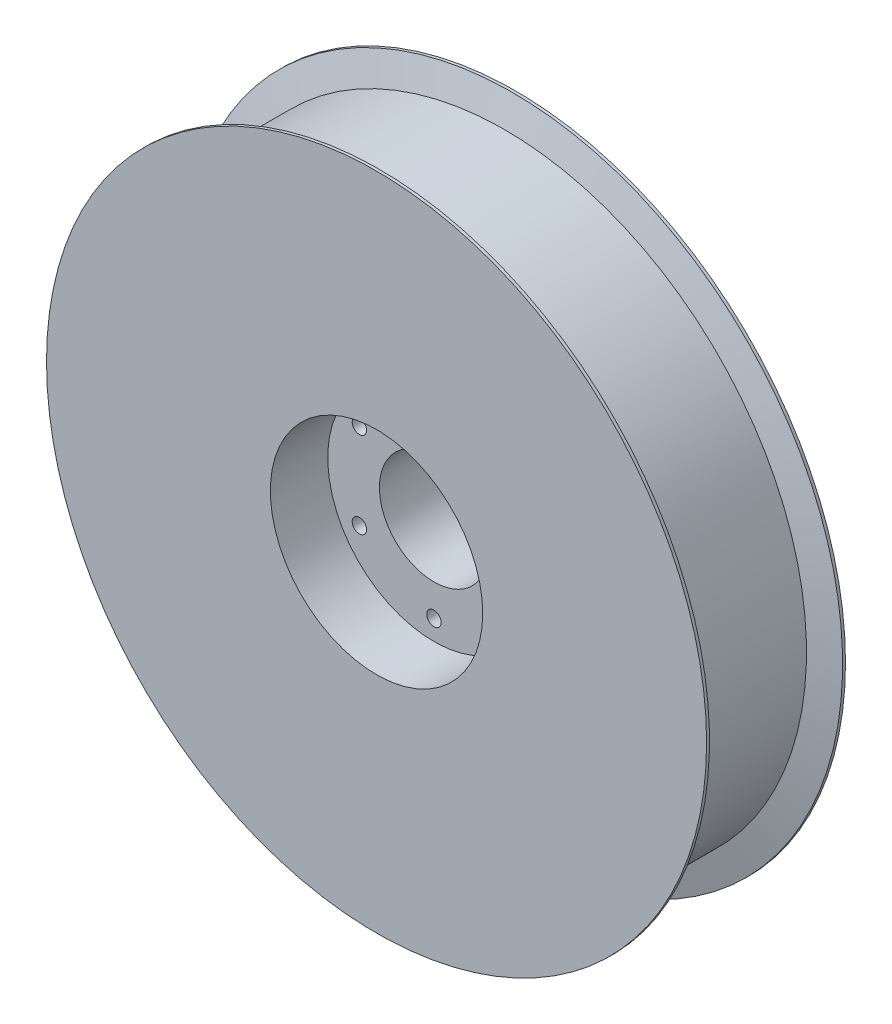
SolidWorks part; units mm, degrees
ref_plane "前基準面" through (0, 0, 0) normal (0, 0, 1) x (1, 0, 0)
ref_plane "上基準面" through (0, 0, 0) normal (0, 1, 0) x (1, 0, 0)
ref_plane "右基準面" through (0, 0, 0) normal (1, 0, 0) x (0, 0, -1)
sketch "草圖1" plane through (0, 0, 0) normal (0, 0, 1) x (1, 0, 0)
  circle A0 centre (0, 0) radius 57.5
  circle A1 centre (0, 0) radius 9.5
  dimension "D1" = 115
  dimension "D2" = 19
extrude "填料-伸長1" add sketch "草圖1" along normal blind 24.2
sketch "草圖3" plane through (0, 0, 24.2) normal (0, 0, 1) x (1, 0, 0)
  circle A0 centre (0, 0) radius 18.5
  circle A1 centre (0, 0) radius 9.5
  circle A2 centre (0, 0) radius 9.5 construction
  dimension "D1" = 37
extrude "除料-伸長2" cut sketch "草圖3" against normal blind 10
sketch "草圖4" plane through (0, 0, 0) normal (0, 0, -1) x (-1, 0, 0)
  line L0 (0, 0) -> (0, 15) construction
  line L1 (0, 0) -> (12.9904, -7.5) construction
  line L2 (0, 0) -> (-12.9904, -7.5) construction
  line L3 (0, 0) -> (12.9904, 7.5) construction
  line L4 (0, 0) -> (0, -15) construction
  line L5 (0, 0) -> (-12.9904, 7.5) construction
  circle A0 centre (0, 0) radius 15 construction
  circle A1 centre (0, 15) radius 1.25
  circle A2 centre (12.9904, -7.5) radius 1.25
  circle A3 centre (-12.9904, -7.5) radius 1.25
  circle A4 centre (12.9904, 7.5) radius 1.25
  circle A5 centre (0, -15) radius 1.25
  circle A6 centre (-12.9904, 7.5) radius 1.25
  dimension "D1" = 30
  dimension "D4" = 2.5
  dimension "D2" = 120
  dimension "D3" = 120
  dimension "D5" = 60
  dimension "D6" = 60
  dimension "D7" = 60
sketch "草圖2" plane through (0, 0, 0) normal (0, 0, -1) x (-1, 0, 0)
  circle A0 centre (0, 0) radius 17.5
  circle A1 centre (0, 0) radius 9.5
  circle A2 centre (0, 0) radius 9.5 construction
  dimension "D1" = 35
extrude "除料-伸長1" [suppressed] cut sketch "草圖2" against normal blind 10
extrude "除料-伸長3" cut sketch "草圖4" against normal through all
sketch "草圖5" plane through (0, 0, 0) normal (0, 1, 0) x (1, 0, 0)
  line L0 (57.5, -23.7) -> (52.555, -22.35)
  line L1 (57.5, -24.2) -> (57.5, 0) construction
  line L2 (52.555, -22.35) -> (52.555, -1.85)
  line L3 (52.555, -1.85) -> (57.5, -0.5)
  line L4 (57.5, -0.5) -> (57.5, -23.7)
  line L5 (0, 0) -> (0, -24.2) construction
  line L6 (-57.5, -24.2) -> (57.5, -24.2) construction
  line L7 (57.5, 0) -> (-57.5, 0) construction
  point P13 (0, 0)
  point P14 (0, 0)
  dimension "D1" = 52.555
  dimension "D2" = 1.85
  dimension "D3" = 1.85
  dimension "D4" = 0.5
  dimension "D5" = 0.5
  dimension "D6" = 57.5
revolve "除料-旋轉1" cut sketch "草圖5" angle 360 about L5
